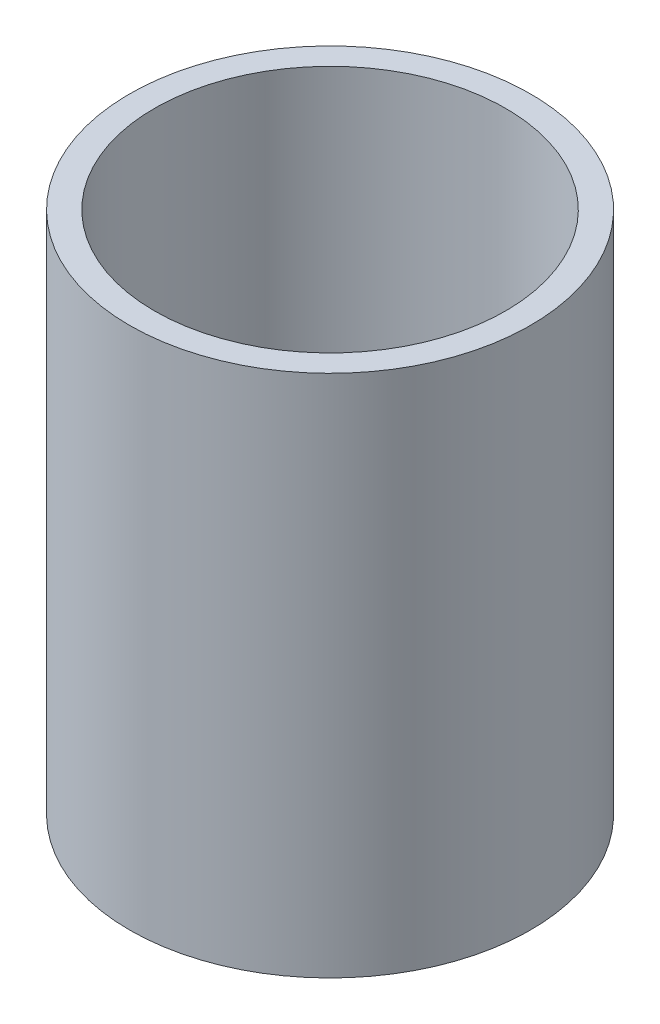
SolidWorks part; units mm, degrees
material "Corrugated Paper"
ref_plane "Front Plane" through (0, 0, 0) normal (0, 0, 1) x (1, 0, 0)
ref_plane "Top Plane" through (0, 0, 0) normal (0, 1, 0) x (1, 0, 0)
ref_plane "Right Plane" through (0, 0, 0) normal (1, 0, 0) x (0, 0, -1)
ref_axis "Axis1" through (0, 55, 0) along (0, -1, 0)
sketch "Sketch1" plane through (0, 0, 0) normal (0, 0, 1) x (1, 0, 0)
  line L1 (-51.054, 45.6176) -> (-44.704, 45.6176)
  line L2 (-51.054, 45.6176) -> (-51.054, -87.7324)
  line L3 (-51.054, -87.7324) -> (-44.704, -87.7324)
  line L4 (-44.704, 45.6176) -> (-44.704, -87.7324)
  line L5 (-38.1, 45.6176) -> (0, 45.6176) construction
  line L6 (-38.1, -87.7324) -> (0, -87.7324) construction
revolve "Revolve1" add sketch "Sketch1" angle 360 about axis through (0, 55, 0) along (0, -1, 0)
